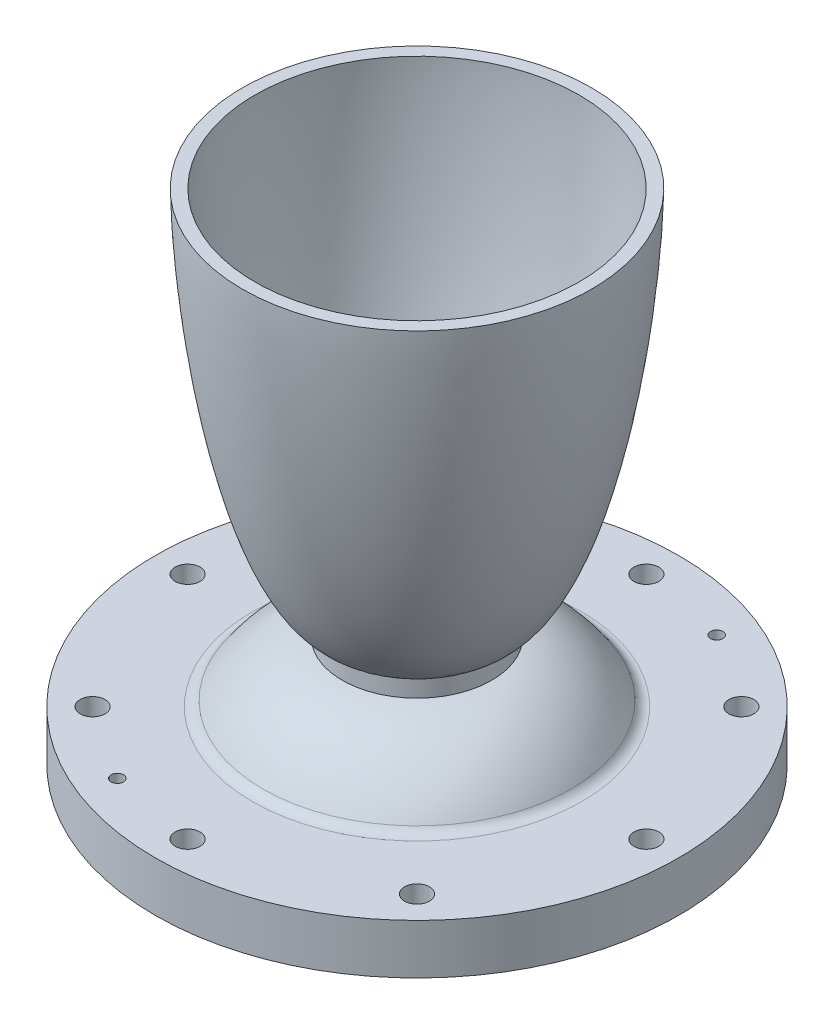
SolidWorks part; units mm, degrees
ref_plane "Front Plane" through (0, 0, 0) normal (0, 0, 1) x (1, 0, 0)
ref_plane "Top Plane" through (0, 0, 0) normal (0, 1, 0) x (1, 0, 0)
ref_plane "Right Plane" through (0, 0, 0) normal (1, 0, 0) x (0, 0, -1)
sketch "Sketch1" plane through (0, 0, 0) normal (0, 0, 1) x (1, 0, 0)
  line L0 (0, 0) -> (0, 127) construction
  line L1 (0, 0) -> (-76.2, 0) construction
  line L2 (0, 25.4) -> (-76.2, 25.4) construction
  line L3 (0, 34.925) -> (-76.2, 34.925) construction
  line L4 (0, 127) -> (-76.2, 127) construction
  line L5 (-41.275, 0) -> (-41.275, 127) construction
  line L6 (-9.525, 0) -> (-9.525, 127) construction
  line L7 (-9.5179, 29.8543) -> (-9.5179, 31.0043)
  line L11 (-41.275, 0) -> (-66.675, 0)
  line L12 (-66.675, 0) -> (-66.675, 12.7)
  line L13 (-44.45, 127) -> (-41.275, 127)
  line L14 (-19.05, 28.0418) -> (-19.05, 32.4773)
  line L15 (-66.675, 12.7) -> (-40.1329, 12.7)
  arc A0 (-9.5179, 29.8543) -> (-13.6663, 25.1315) centre (-14.2804, 29.8543) cw
  arc A1 (-12.6773, 35.4889) -> (-9.5179, 31.0043) centre (-14.2804, 31.0043) cw
  spline S0 degree 4 poles (-41.275, 0) (-41.274, 0.0486) (-41.2703, 0.1458) (-41.2499, 0.4207) (-41.1845, 0.9521) (-41.0457, 1.7182) (-40.8031, 2.7106) (-40.4714, 3.7959) (-40.0739, 4.8928) (-39.5825, 6.0748) (-38.9093, 7.4952) (-38.0132, 9.1298) (-36.851, 10.946) (-35.4547, 12.8169) (-33.9314, 14.5858) (-32.2904, 16.2459) (-30.5401, 17.7904) (-28.6887, 19.2123) (-26.7446, 20.5043) (-24.7162, 21.6597) (-22.6125, 22.6717) (-20.4432, 23.534) (-18.4963, 24.1525) (-16.7999, 24.5824) (-15.5134, 24.8436) (-14.652, 24.992) (-13.9295, 25.0983) (-13.3539, 25.1729) (-12.7691, 25.2371) (-12.1975, 25.2908) (-11.6002, 25.334) (-11.0462, 25.3667) (-10.5221, 25.3848) (-10.2205, 25.3937) (-9.8178, 25.3983) (-9.4782, 25.4019) (-8.766, 25.3965) (-7.8642, 25.3656) (-6.771, 25.2903) (-5.943, 25.2058) (-5.4011, 25.137) (-5.1262, 25.0995) knots 0 0 0 0 0 0.004015 0.00803 0.022747 0.044178 0.068247 0.092317 0.116386 0.140456 0.173884 0.222023 0.270162 0.318301 0.36644 0.414579 0.462719 0.510858 0.558997 0.607136 0.655275 0.703414 0.751553 0.775623 0.799692 0.811727 0.823762 0.835797 0.847831 0.859866 0.871901 0.883936 0.89597 0.899251 0.902531 0.909092 0.931819 0.954546 0.977273 1 1 1 1 1 construction
  spline S1 degree 4 poles (-41.275, 0) (-41.274, 0.0486) (-41.2703, 0.1458) (-41.2499, 0.4207) (-41.1845, 0.9521) (-41.0457, 1.7182) (-40.8031, 2.7106) (-40.4714, 3.7959) (-40.0739, 4.8928) (-39.5825, 6.0748) (-38.9093, 7.4952) (-38.0132, 9.1298) (-36.851, 10.946) (-35.4547, 12.8169) (-33.9314, 14.5858) (-32.2904, 16.2459) (-30.5401, 17.7904) (-28.6887, 19.2123) (-26.7446, 20.5043) (-24.7162, 21.6597) (-22.6125, 22.6717) (-20.4432, 23.534) (-18.4963, 24.1525) (-16.7999, 24.5824) (-15.5134, 24.8436) (-14.6582, 24.9909) (-14.0865, 25.0752) (-13.8044, 25.1136) (-13.6663, 25.1315) knots 0 0 0 0 0 0.004015 0.00803 0.022747 0.044178 0.068247 0.092317 0.116386 0.140456 0.173884 0.222023 0.270162 0.318301 0.36644 0.414579 0.462719 0.510858 0.558997 0.607136 0.655275 0.703414 0.751553 0.775623 0.799692 0.811727 0.823244 0.823244 0.823244 0.823244 0.823244
  spline S2 degree 4 poles (-41.275, 127) (-41.2689, 126.1614) (-41.223, 124.4846) (-41.0734, 121.0785) (-40.7228, 115.949) (-40.1705, 109.9396) (-39.3608, 103.0591) (-38.3822, 96.2006) (-37.2306, 89.369) (-35.8956, 82.5706) (-34.3591, 75.8148) (-32.5938, 69.1146) (-30.5585, 62.4908) (-28.1913, 55.9764) (-25.6831, 50.2918) (-23.1258, 45.5925) (-20.7112, 42.0555) (-18.7203, 39.6859) (-17.0528, 38.1035) (-15.7469, 37.1002) (-14.7707, 36.4765) (-14.0774, 36.0905) (-13.4074, 35.7704) (-12.7662, 35.5114) (-12.1434, 35.3055) (-11.5442, 35.1486) (-11.0256, 35.048) (-10.6005, 34.9876) (-10.2387, 34.9525) (-9.9404, 34.9337) (-9.6298, 34.9237) (-9.3404, 34.9245) (-8.9827, 34.9383) (-8.6161, 34.9673) (-8.2594, 35.0109) (-7.9015, 35.0689) (-7.453, 35.1595) (-6.8882, 35.3045) (-6.2156, 35.5254) (-5.3966, 35.8667) (-4.53, 36.3129) (-3.8846, 36.7116) (-3.4379, 37.0182) (-3.2182, 37.1769) knots 0 0 0 0 0 0.030812 0.061623 0.12525 0.188877 0.252504 0.316131 0.379757 0.443384 0.507011 0.570638 0.634265 0.697892 0.761519 0.798698 0.830511 0.855004 0.875012 0.882966 0.890919 0.897534 0.90415 0.910229 0.916309 0.921611 0.926913 0.929564 0.932215 0.934867 0.937518 0.940824 0.944131 0.947438 0.950745 0.954114 0.957484 0.964223 0.97216 0.980096 0.990048 1 1 1 1 1 construction
  spline S3 degree 4 poles (-41.275, 127) (-41.2689, 126.1614) (-41.223, 124.4846) (-41.0734, 121.0785) (-40.7228, 115.949) (-40.1705, 109.9396) (-39.3608, 103.0591) (-38.3822, 96.2006) (-37.2306, 89.369) (-35.8956, 82.5706) (-34.3591, 75.8148) (-32.5938, 69.1146) (-30.5585, 62.4908) (-28.1913, 55.9764) (-25.6831, 50.2918) (-23.1258, 45.5925) (-20.7112, 42.0555) (-18.7203, 39.6859) (-17.0528, 38.1035) (-15.7469, 37.1002) (-14.7707, 36.4765) (-14.0774, 36.0905) (-13.4648, 35.7979) (-13.0376, 35.6216) (-12.7733, 35.5232) (-12.6773, 35.4889) knots 0 0 0 0 0 0.030812 0.061623 0.12525 0.188877 0.252504 0.316131 0.379757 0.443384 0.507011 0.570638 0.634265 0.697892 0.761519 0.798698 0.830511 0.855004 0.875012 0.882966 0.890919 0.897534 0.90415 0.907893 0.907893 0.907893 0.907893 0.907893
  spline S4 degree 4 poles (-44.45, 127) (-44.444, 126.0899) (-44.3997, 124.27) (-44.2562, 120.6046) (-43.9212, 115.0986) (-43.395, 108.6661) (-42.6246, 101.3148) (-41.6912, 93.9824) (-40.5889, 86.6733) (-39.3055, 79.3937) (-37.8196, 72.1526) (-36.0989, 64.963) (-34.093, 57.8471) (-31.7662, 50.972) (-29.315, 45.1286) (-26.8381, 40.4693) (-24.5703, 37.1783) (-22.7831, 35.133) (-21.3073, 33.8365) (-20.1932, 33.0738) (-19.3831, 32.6276) (-18.8014, 32.3576) (-18.24, 32.1443) (-17.7056, 31.9828) (-17.2391, 31.8782) (-16.8521, 31.815) (-16.5271, 31.7785) (-16.26, 31.759) (-15.9995, 31.7494) (-15.7743, 31.7491) (-15.5273, 31.7574) (-15.2825, 31.7735) (-14.9713, 31.8052) (-14.5939, 31.8625) (-14.1334, 31.9598) (-13.603, 32.1134) (-13.0484, 32.3164) (-12.4762, 32.5733) (-11.8579, 32.9033) (-11.2026, 33.3155) (-10.7145, 33.6712) (-10.3753, 33.941) (-10.2085, 34.0795) knots 0 0 0 0 0 0.033161 0.066322 0.133645 0.200968 0.268291 0.335614 0.402937 0.47026 0.537583 0.604906 0.672229 0.739552 0.80187 0.835532 0.864104 0.884898 0.900578 0.906888 0.913199 0.918565 0.923931 0.92874 0.933549 0.935917 0.938286 0.940654 0.943023 0.945188 0.947354 0.94952 0.951685 0.956526 0.961366 0.966591 0.971816 0.978012 0.984208 0.992104 1 1 1 1 1 construction
  spline S5 degree 4 poles (-44.45, 127) (-44.444, 126.0899) (-44.3997, 124.27) (-44.2562, 120.6046) (-43.9212, 115.0986) (-43.395, 108.6661) (-42.6246, 101.3148) (-41.6912, 93.9824) (-40.5889, 86.6733) (-39.3055, 79.3937) (-37.8196, 72.1526) (-36.0989, 64.963) (-34.093, 57.8471) (-31.7662, 50.972) (-29.315, 45.1286) (-26.8381, 40.4693) (-24.5703, 37.1783) (-22.7831, 35.133) (-21.3073, 33.8365) (-20.1947, 33.0748) (-19.5153, 32.7005) (-19.2058, 32.5488) (-19.05, 32.4773) knots 0 0 0 0 0 0.033161 0.066322 0.133645 0.200968 0.268291 0.335614 0.402937 0.47026 0.537583 0.604906 0.672229 0.739552 0.80187 0.835532 0.864104 0.884898 0.900578 0.906888 0.913134 0.913134 0.913134 0.913134 0.913134
  spline S6 degree 4 poles (-41.2576, 10.617) (-41.2217, 10.6882) (-41.1523, 10.8253) (-41.0377, 11.055) (-40.7899, 11.5207) (-40.6166, 11.8513) (-40.2377, 12.5205) (-40.0785, 12.7954) (-39.7598, 13.331) (-39.5464, 13.6751) (-39.2217, 14.1904) (-38.9146, 14.6561) (-38.5835, 15.1439) (-38.1864, 15.7058) (-37.7751, 16.2686) (-37.2844, 16.9097) (-36.7028, 17.6308) (-36.1034, 18.3345) (-35.4848, 19.0229) (-34.8481, 19.6936) (-34.1927, 20.3469) (-33.5194, 20.9811) (-32.828, 21.5958) (-31.963, 22.3205) (-31.0704, 23.0114) (-30.151, 23.6661) (-29.2055, 24.2824) (-28.4146, 24.7622) (-27.608, 25.2156) (-26.7869, 25.6414) (-25.9509, 26.0388) (-25.1026, 26.4064) (-24.24, 26.7437) (-23.3684, 27.049) (-22.4814, 27.3225) (-21.7046, 27.5316) (-21.021, 27.6912) (-20.4682, 27.8071) (-19.9867, 27.8962) (-19.6298, 27.9578) (-19.1569, 28.0277) (-18.9276, 28.0586) (-18.5178, 28.1099) (-18.2348, 28.1388) (-17.8736, 28.1736) (-17.5514, 28.1982) (-17.206, 28.2209) (-16.8716, 28.2372) (-16.6149, 28.2464) (-16.4458, 28.2507) (-16.3613, 28.2524) knots 0 0 0 0 0 0.009223 0.018447 0.036893 0.05534 0.073786 0.088217 0.102648 0.117078 0.131509 0.16037 0.174801 0.189231 0.218092 0.246954 0.275815 0.304676 0.333537 0.362399 0.39126 0.420121 0.448982 0.477843 0.532083 0.560945 0.589806 0.618667 0.647528 0.676389 0.705251 0.734112 0.762973 0.791834 0.820695 0.849557 0.863987 0.878418 0.892848 0.907279 0.915799 0.926262 0.936724 0.947187 0.957649 0.968237 0.978825 0.989412 1 1 1 1 1 construction
  spline S7 degree 4 poles (-40.1329, 12.7) (-40.084, 12.7842) (-39.9833, 12.9554) (-39.7598, 13.331) (-39.5464, 13.6751) (-39.2217, 14.1904) (-38.9146, 14.6561) (-38.5835, 15.1439) (-38.1864, 15.7058) (-37.7751, 16.2686) (-37.2844, 16.9097) (-36.7028, 17.6308) (-36.1034, 18.3345) (-35.4848, 19.0229) (-34.8481, 19.6936) (-34.1927, 20.3469) (-33.5194, 20.9811) (-32.828, 21.5958) (-31.963, 22.3205) (-31.0704, 23.0114) (-30.151, 23.6661) (-29.2055, 24.2824) (-28.4146, 24.7622) (-27.608, 25.2156) (-26.7869, 25.6414) (-25.9509, 26.0388) (-25.1026, 26.4064) (-24.24, 26.7437) (-23.3684, 27.049) (-22.4814, 27.3225) (-21.7046, 27.5316) (-21.021, 27.6912) (-20.4682, 27.8071) (-19.9867, 27.8962) (-19.6298, 27.9578) (-19.2603, 28.0124) (-19.1069, 28.034) (-19.05, 28.0418) knots 0.073786 0.073786 0.073786 0.073786 0.073786 0.088217 0.102648 0.117078 0.131509 0.16037 0.174801 0.189231 0.218092 0.246954 0.275815 0.304676 0.333537 0.362399 0.39126 0.420121 0.448982 0.477843 0.532083 0.560945 0.589806 0.618667 0.647528 0.676389 0.705251 0.734112 0.762973 0.791834 0.820695 0.849557 0.863987 0.878418 0.892848 0.907279 0.915799 0.915799 0.915799 0.915799 0.915799
  dimension "D9" = 4.7625
  dimension "D10" = 4.7625
  dimension "D1" = 127
  dimension "D3" = 41.275
  dimension "D4" = 25.4
  dimension "D5" = 9.525
  dimension "D6" = 9.525
  dimension "D7" = 66.675
  dimension "D8" = 12.7
revolve "Main Revolve" add sketch "Sketch1" angle 360 about L0
fillet "Converging Fillet" radius 3.175 1 edges at (0, 12.7, -40.1329)
sketch "Sketch for Bolt Holes" plane through (0, 12.7, 0) normal (0, 1, 0) x (1, 0, 0)
  circle A0 centre (0, 0) radius 58.42
  circle A1 centre (-58.42, 0) radius 3.175
  circle A2 centre (-41.3092, 41.3092) radius 3.175
  circle A3 centre (0, 58.42) radius 3.175
  circle A4 centre (41.3092, 41.3092) radius 3.175
  circle A5 centre (58.42, 0) radius 3.175
  circle A6 centre (41.3092, -41.3092) radius 3.175
  circle A7 centre (0, -58.42) radius 3.175
  circle A8 centre (-41.3092, -41.3092) radius 3.175
  point P22 (0, 0)
  dimension "D1" = 116.84
  dimension "D2" = 6.35
  dimension "D3" = 8
hole_wizard "Bolt Holes" positions "Sketch3" profile "Sketch4" hole size "1/4" standard "ANSI Inch"
sketch "Sketch3" plane through (0, 12.7, 0) normal (0, 1, 0) x (1, 0, 0)
  point P0 (-58.42, 0)
  point P3 (-41.3092, 41.3092)
  point P6 (0, 58.42)
  point P9 (41.3092, 41.3092)
  point P12 (58.42, 0)
  point P15 (41.3092, -41.3092)
  point P18 (0, -58.42)
  point P21 (-41.3092, -41.3092)
sketch "Sketch4" plane through (-58.42, 12.7, 0) normal (1, 0, 0) x (0, 0, 1)
  line L0 (0, 0) -> (0, 14.6077)
  line L1 (0, 14.6077) -> (3.175, 12.7)
  line L2 (3.175, 12.7) -> (3.175, 0)
  line L5 (3.175, 0) -> (0, 0)
  line L10 (0, 14.6077) -> (-3.175, 12.7) construction
  line L11 (0, -6.35) -> (0, 107.95) construction
  dimension "Hole Dia." = 6.35
  dimension "Hole Depth" = 12.7
  dimension "Drill Angle" = 118
sketch "Sketch for Pin Holes" plane through (0, 0, 0) normal (0, -1, 0) x (1, 0, 0)
  line L0 (0, 0) -> (0, -69.4939) construction
  line L1 (0, 0) -> (29.6148, -71.4963) construction
  circle A0 centre (0, 0) radius 58.42
  circle A1 centre (22.3564, -53.973) radius 3.175
  circle A2 centre (-22.3564, 53.973) radius 3.175
  point P11 (0, 0)
  dimension "D2" = 6.35
  dimension "D1" = 22.5
  dimension "D3" = 2
hole_wizard "Pin Holes" positions "Sketch6" profile "Sketch7" legacy
sketch "Sketch6" plane through (0, 0, 0) normal (0, -1, 0) x (-1, 0, 0)
  point P0 (-22.3564, 53.973)
  point P3 (22.3564, -53.973)
sketch "Sketch7" plane through (22.3564, 0, -53.973) normal (1, 0, 0) x (0, 0, -1)
  line L0 (0, 0) -> (0, 100)
  line L1 (0, 100) -> (1.5875, 100)
  line L2 (1.5875, 100) -> (1.5875, 6.35)
  line L3 (1.5875, 6.35) -> (3.175, 6.35)
  line L4 (3.175, 6.35) -> (3.175, 0)
  line L5 (3.175, 0) -> (0, 0)
  line L6 (0, 110) -> (0, -10) construction
  dimension "Diameter" = 3.175
  dimension "Depth" = 100
  dimension "C-Bore Diameter" = 6.35
  dimension "C-Bore Depth" = 6.35
